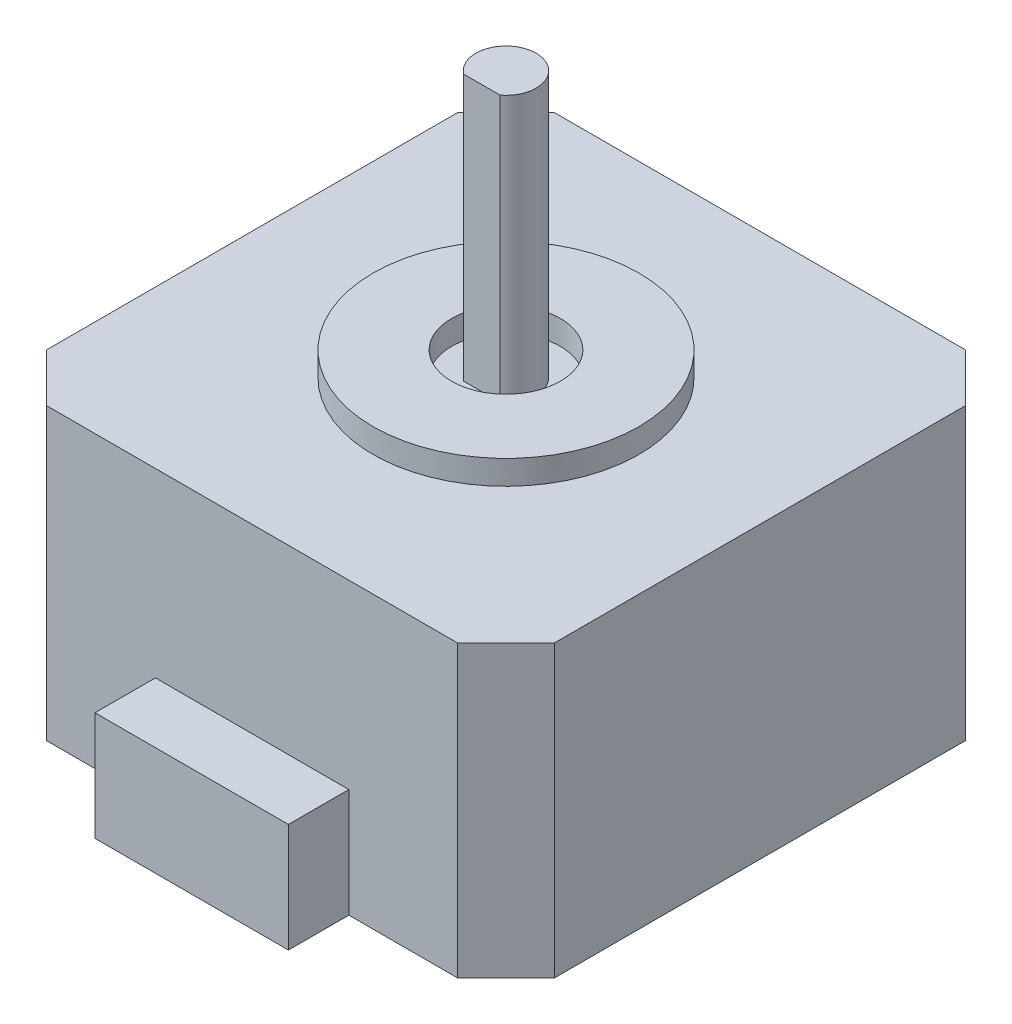
SolidWorks part; units mm, degrees
ref_plane "Front Plane" through (0, 0, 0) normal (0, 0, 1) x (1, 0, 0)
ref_plane "Top Plane" through (0, 0, 0) normal (0, 1, 0) x (1, 0, 0)
ref_plane "Right Plane" through (0, 0, 0) normal (1, 0, 0) x (0, 0, -1)
sketch "Sketch1" plane through (0, 0, 0) normal (0, 1, 0) x (1, 0, 0)
  line L1 (0, 0) -> (42, 0)
  line L2 (0, 0) -> (0, 42)
  line L3 (0, 42) -> (42, 42)
  line L4 (42, 0) -> (42, 42)
  dimension "D1" = 42
  dimension "D2" = 42
extrude "Boss-Extrude1" add sketch "Sketch1" along normal blind 24
sketch "Sketch2" plane through (0, 0, 0) normal (0, 0, 1) x (1, 0, 0)
  line L0 (0, 0) -> (42, 0) construction
  line L1 (13, 0) -> (29, 0)
  line L2 (13, 0) -> (13, 9)
  line L3 (13, 9) -> (29, 9)
  line L4 (29, 0) -> (29, 9)
  line L5 (0, 24) -> (0, 0) construction
  dimension "D1" = 9
  dimension "D2" = 16
  dimension "D3" = 13
extrude "Boss-Extrude2" add sketch "Sketch2" along normal blind 5
sketch "Sketch3" plane through (0, 24, 0) normal (0, 1, 0) x (1, 0, 0)
  line L0 (0, 42) -> (0, 0) construction
  line L1 (0, 0) -> (42, 0) construction
  circle A0 centre (21, 21) radius 11
  circle A1 centre (21, 21) radius 4.5
  dimension "D1" = 22
  dimension "D4" = 9
  dimension "D2" = 21
  dimension "D3" = 21
extrude "Boss-Extrude4" add sketch "Sketch3" along normal blind 2
sketch "Sketch4" plane through (0, 24, 0) normal (0, 1, 0) x (1, 0, 0)
  line L0 (0, 42) -> (0, 0) construction
  line L1 (0, 0) -> (42, 0) construction
  line L2 (19.5, 19) -> (22.5, 19)
  arc A0 (22.5, 19) -> (19.5, 19) centre (21, 21) ccw
  dimension "D3" = 5
  dimension "D1" = 21
  dimension "D2" = 21
  dimension "D4" = 2
extrude "Boss-Extrude5" add sketch "Sketch4" along normal blind 22
chamfer "Chamfer1" distance 4 1 edges at (0, 12, 0)
chamfer "Chamfer2" distance 4 1 edges at (42, 12, 0)
chamfer "Chamfer3" distance 4 1 edges at (42, 12, -42)
chamfer "Chamfer4" distance 4 1 edges at (0, 12, -42)
